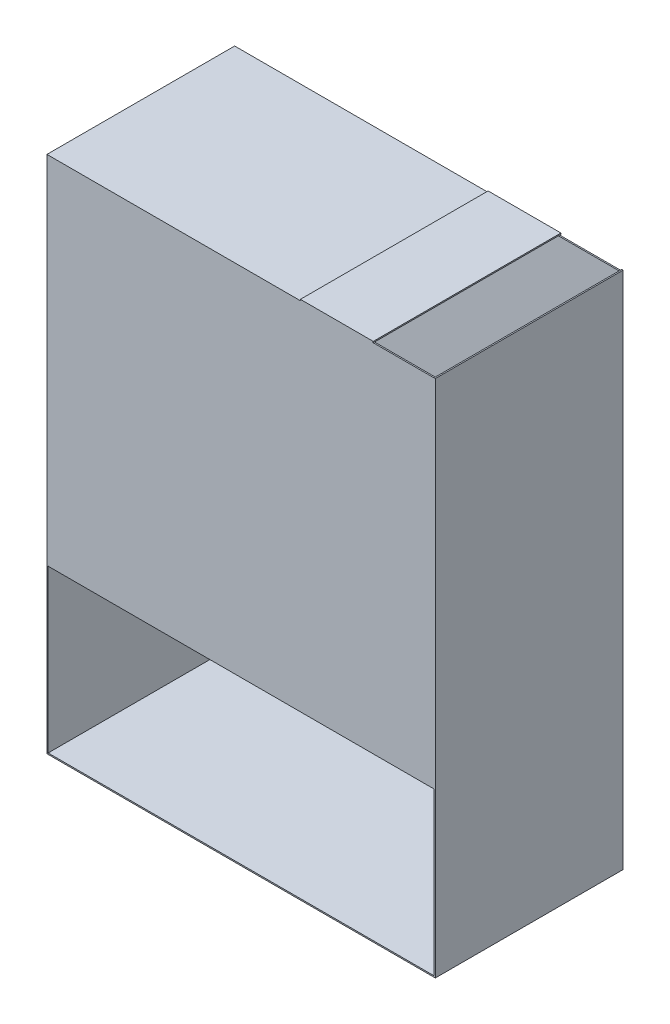
SolidWorks part; units mm, degrees
ref_plane "前视基准面" through (0, 0, 0) normal (0, 0, 1) x (1, 0, 0)
ref_plane "上视基准面" through (0, 0, 0) normal (0, 1, 0) x (1, 0, 0)
ref_plane "右视基准面" through (0, 0, 0) normal (1, 0, 0) x (0, 0, -1)
sketch "草图1" plane through (0, 0, 0) normal (0, 0, 1) x (1, 0, 0)
  line L0 (0, 801.8755) -> (1.8755, 801.8755)
  line L1 (0, 0) -> (600, 0)
  line L2 (0, 0) -> (0, 1.8755)
  line L3 (1.8755, 2) -> (598, 2)
  line L4 (600, 0) -> (600, 1.8718)
  line L6 (0, 1.8755) -> (0, 801.8755)
  line L8 (1.8755, 2) -> (1.8755, 800)
  line L10 (600, 1.8718) -> (600, 802)
  line L11 (600, 802) -> (598, 802)
  line L12 (598, 2) -> (598, 802)
  line L21 (1.8755, 801.8755) -> (391.5337, 801.8755)
  line L22 (1.8755, 800) -> (451.9871, 800)
  line L23 (451.9871, 801.8755) -> (451.9871, 800)
  line L24 (451.9871, 801.8755) -> (504.0616, 801.8755)
  line L25 (391.5337, 801.8755) -> (391.5337, 803.7509)
  line L26 (391.5337, 803.7509) -> (504.0616, 803.7509)
  line L27 (504.0616, 801.8755) -> (504.0616, 803.7509)
  dimension "D1" = 2
  dimension "D2" = 2
extrude "凸台-拉伸1" add sketch "草图1" along normal blind 290
sketch "草图2" plane through (0, 0, 0) normal (0, 1, 0) x (1, 0, 0)
  line L0 (598, -290) -> (598, 0) construction
  line L1 (0, 0) -> (598, 0)
  line L2 (0, 0) -> (0, -2)
  line L3 (0, -2) -> (598, -2)
  line L4 (598, 0) -> (598, -2)
extrude "凸台-拉伸2" add sketch "草图2" along normal blind 800
sketch "草图3" plane through (0, 0, 0) normal (0, 1, 0) x (1, 0, 0)
  line L0 (600, -290) -> (600, 0) construction
  line L1 (0, -290) -> (600, -290)
  line L2 (0, -290) -> (0, -288)
  line L3 (0, -288) -> (600, -288)
  line L4 (600, -290) -> (600, -288)
extrude "凸台-拉伸3" add sketch "草图3" against normal blind 550 from surface at 801.8755 starting at face at (195.7668, 801.8755, 145)
